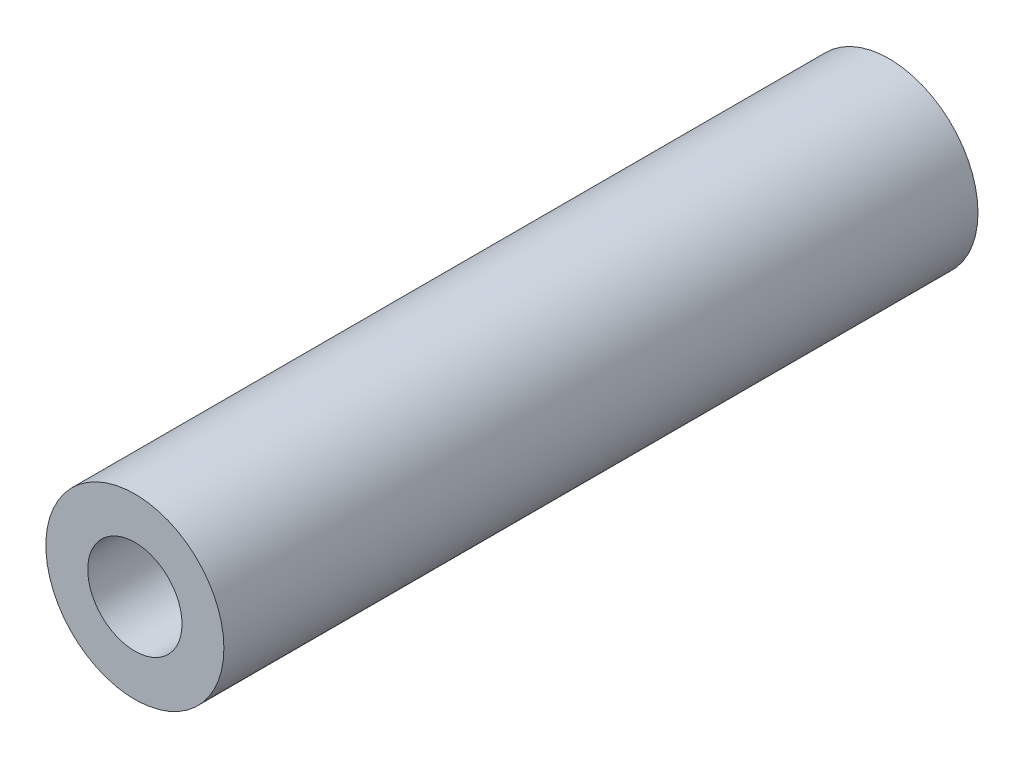
SolidWorks part; units mm, degrees
ref_plane "前视基准面" through (0, 0, 0) normal (0, 0, 1) x (1, 0, 0)
ref_plane "上视基准面" through (0, 0, 0) normal (0, 1, 0) x (1, 0, 0)
ref_plane "右视基准面" through (0, 0, 0) normal (1, 0, 0) x (0, 0, -1)
other "Configuration Table"
sketch "草图1" plane through (0, 0, 0) normal (0, 0, 1) x (1, 0, 0)
  circle A0 centre (0, 0) radius 2.25
  circle A1 centre (0, 0) radius 4.25
  point P3 (0, 0)
  dimension "D1" = 4.5
  dimension "D2" = 2
extrude "凸台-拉伸1" add sketch "草图1" along normal blind 36
